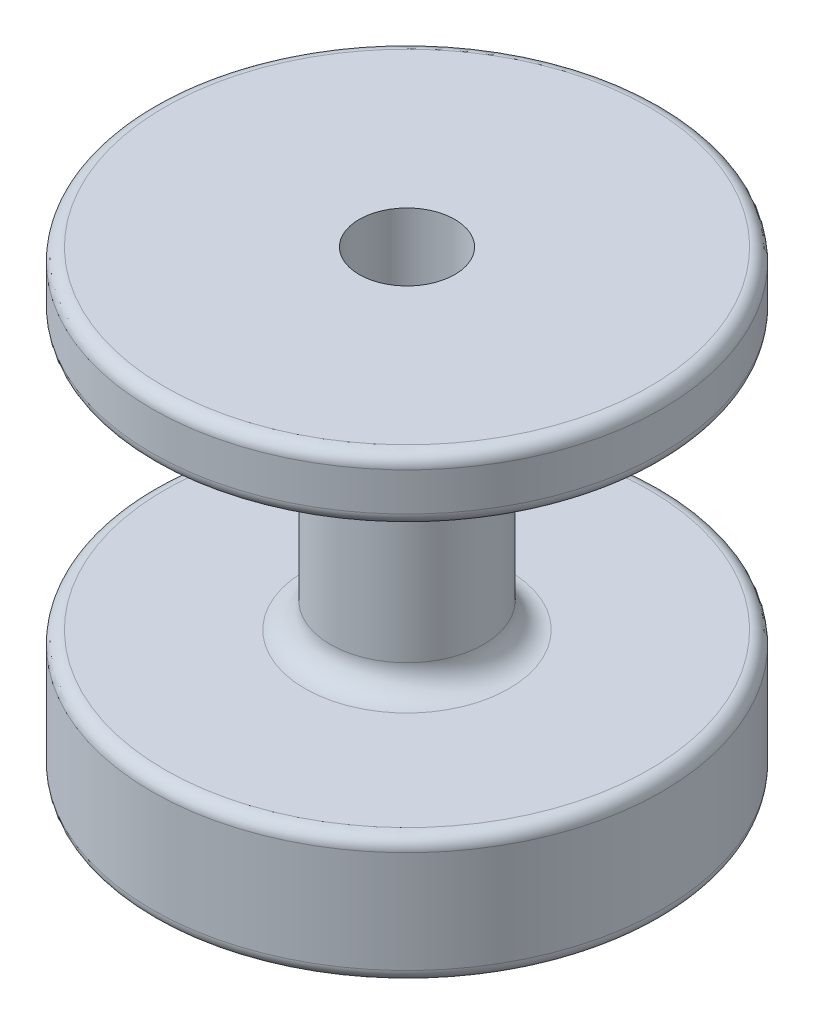
SolidWorks part; units mm, degrees
material "自定义塑料"
ref_plane "前视基准面" through (0, 0, 0) normal (0, 0, 1) x (1, 0, 0)
ref_plane "上视基准面" through (0, 0, 0) normal (0, 1, 0) x (1, 0, 0)
ref_plane "右视基准面" through (0, 0, 0) normal (1, 0, 0) x (0, 0, -1)
sketch "草图1" plane through (0, 0, 0) normal (0, 1, 0) x (1, 0, 0)
  circle A0 centre (0, 0) radius 20
  dimension "D1" = 40
extrude "凸台-拉伸1" add sketch "草图1" along normal blind 36
sketch "草图2" plane through (0, 0, 0) normal (0, 1, 0) x (1, 0, 0)
  circle A0 centre (0, 0) radius 20
  circle A2 centre (0, 0) radius 6
  circle A3 centre (0, 0) radius 1.6513
  dimension "D1" = 12
  dimension "D2" = 40
extrude "切除-拉伸1" cut sketch "草图2" along normal blind 21 from offset 10 contours A0 A2
sketch "草图5" plane through (0, 0, 0) normal (0, 1, 0) x (1, 0, 0)
  circle A0 centre (0, 0) radius 4.5
  dimension "D1" = 9
extrude "凸台-拉伸2" [suppressed] add sketch "草图5" against normal blind 10
sketch "草图4" plane through (0, 0, 0) normal (0, 1, 0) x (1, 0, 0)
  circle A0 centre (0, 0) radius 2
  dimension "D1" = 4
extrude "切除-拉伸3" cut sketch "草图4" against normal blind 47 and the other way blind 47 contours A0
sketch "草图3" plane through (0, 36, 0) normal (0, 1, 0) x (1, 0, 0)
  circle A0 centre (0, 0) radius 3.75
  dimension "D1" = 7.5
extrude "切除-拉伸7" cut sketch "草图3" against normal blind 17
sketch "草图6" plane through (0, 0, 0) normal (0, 1, 0) x (1, 0, 0)
  circle A0 centre (0, 0) radius 21.25
  dimension "D1" = 42.5
fillet "圆角1" radius 2 2 edges at (0, 10, 6) (0, 31, 6)
fillet "圆角2" radius 1 4 edges at (0, 36, 20) (0, 31, 20) (0, 10, 20) (0, 0, 20)
